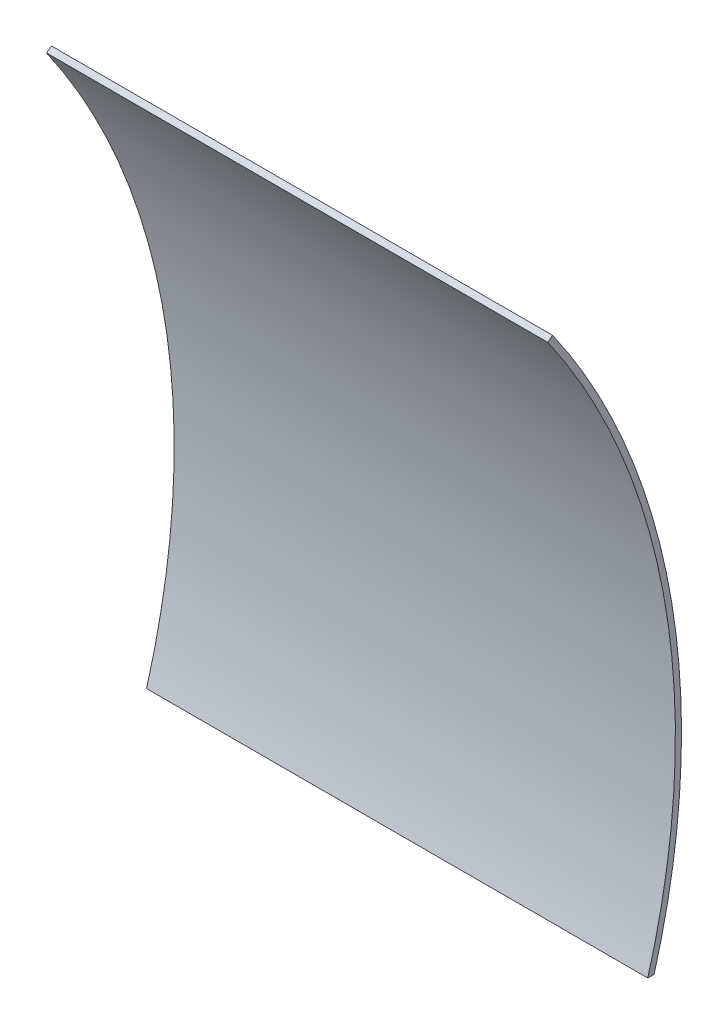
SolidWorks part; units mm, degrees
material "PE High Density"
ref_plane "Front Plane" through (0, 0, 0) normal (0, 0, 1) x (1, 0, 0)
ref_plane "Top Plane" through (0, 0, 0) normal (0, 1, 0) x (1, 0, 0)
ref_plane "Right Plane" through (0, 0, 0) normal (1, 0, 0) x (0, 0, -1)
sketch "Sketch1" plane through (0, 0, 0) normal (1, 0, 0) x (0, 0, -1)
  line L0 (0, 0) -> (183.3562, 0) construction
  line L1 (0, 0) -> (150.1966, 105.1688) construction
  line L2 (183.3562, 0) -> (183.3562, -50.8) construction
  line L3 (183.3562, -50.8) -> (176.1785, -50.8) construction
  line L4 (150.1966, 105.1688) -> (151.4971, 106.0794) construction
  line L5 (176.1785, -50.8) -> (177.8301, -50.8)
  line L6 (150.1966, 105.1688) -> (151.4971, 106.0794)
  arc A0 (183.3562, 0) -> (150.1966, 105.1688) centre (0, 0) ccw
  arc A1 (183.3562, 0) -> (176.1785, -50.8) centre (0, 0) cw
  arc A2 (177.8301, -50.8) -> (151.4971, 106.0794) centre (0, 0) ccw
  dimension "D2" = 35
  dimension "D4" = 1.5875
  dimension "D1" = 183.3562
  dimension "D3" = 50.8
extrude "Boss-Extrude1" add sketch "Sketch1" along normal blind 130.175
